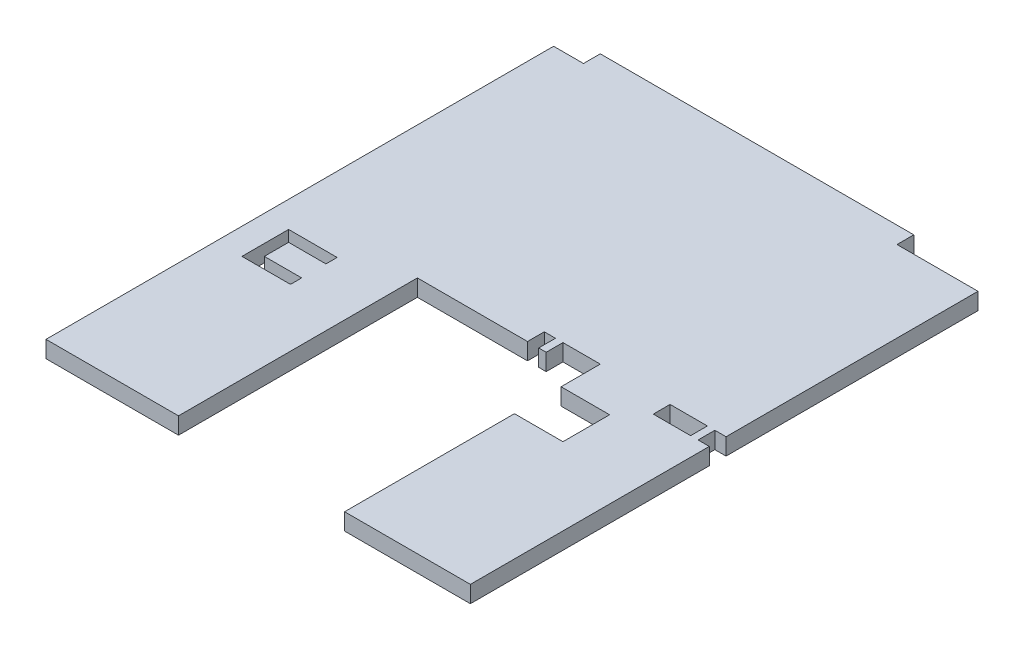
SolidWorks part; units mm, degrees
material "Teak"
ref_plane "Front Plane" through (0, 0, 0) normal (0, 0, 1) x (1, 0, 0)
ref_plane "Top Plane" through (0, 0, 0) normal (0, 1, 0) x (1, 0, 0)
ref_plane "Right Plane" through (0, 0, 0) normal (1, 0, 0) x (0, 0, -1)
sketch "Sketch1" plane through (0, 0, 0) normal (0, 1, 0) x (1, 0, 0)
  line L0 (-33.7045, -15.5) -> (-33.7045, -18.5) construction
  line L1 (46.2955, 72) -> (38.2955, 72) construction
  line L2 (38.2955, 72) -> (38.2955, 76.5) construction
  line L3 (-45.7045, 76.5) -> (-45.7045, 72) construction
  line L4 (-45.7045, 72) -> (-53.7045, 72) construction
  line L5 (-53.7045, -64) -> (-53.7045, 72) construction
  line L6 (-18.2045, -64) -> (-53.7045, -64) construction
  line L7 (-18.2045, -64) -> (-18.2045, 0) construction
  line L8 (-18.2045, 0) -> (11.2955, 0) construction
  line L9 (14.2955, 0) -> (16.2955, 0) construction
  line L10 (26.2955, 0) -> (26.2955, -6) construction
  line L11 (26.2955, -18.5) -> (26.2955, -60) construction
  line L12 (-33.7045, -15.5) -> (-43.7045, -15.5) construction
  line L13 (-46.7045, -6) -> (-33.7045, -6) construction
  line L14 (-46.7045, -18.5) -> (-33.7045, -18.5) construction
  line L15 (-33.7045, -6) -> (-33.7045, -9) construction
  line L16 (-33.7045, -9) -> (-43.7045, -9) construction
  line L17 (39.2955, -6) -> (26.2955, -6) construction
  line L18 (39.2955, -18.5) -> (26.2955, -18.5) construction
  line L19 (-45.7045, 76.5) -> (38.2955, 76.5) construction
  line L20 (26.2955, -60) -> (26.2955, -64) construction
  line L21 (26.2955, -64) -> (46.2955, -64) construction
  line L22 (-46.7045, -6) -> (-46.7045, -18.5) construction
  line L23 (-43.7045, -9) -> (-43.7045, -15.5) construction
  line L24 (39.2955, -6) -> (39.2955, -18.5) construction
  line L25 (46.2955, -64) -> (51.2955, -64) construction
  line L26 (51.2955, 72) -> (46.2955, 72) construction
  line L27 (26.2955, 0) -> (26.2955, 4.5) construction
  line L28 (26.2955, 4.5) -> (16.2955, 4.5) construction
  line L29 (16.2955, 4.5) -> (16.2955, 0) construction
  line L30 (16.2955, 0) -> (14.2955, 0) construction
  line L31 (59.9955, 4.5) -> (56.9955, 4.5) construction
  line L32 (56.9955, 4.5) -> (56.9955, 0) construction
  line L33 (26.2955, -64) -> (51.2955, -64) construction
  line L34 (51.2955, -64) -> (59.9955, -64) construction
  line L35 (59.9955, -64) -> (59.9955, 0) construction
  line L36 (59.9955, 4.5) -> (59.9955, 72) construction
  line L37 (59.9955, 72) -> (51.2955, 72) construction
  line L38 (54.9955, 0) -> (54.9955, 4.5) construction
  line L39 (54.9955, 4.5) -> (44.9955, 4.5) construction
  line L40 (44.9955, 4.5) -> (44.9955, 0) construction
  line L41 (14.2955, 0) -> (14.2955, 4.5) construction
  line L42 (14.2955, 4.5) -> (11.2955, 4.5) construction
  line L43 (11.2955, 4.5) -> (11.2955, 0) construction
  line L44 (44.9955, 0) -> (54.9955, 0) construction
  line L45 (56.9955, 0) -> (59.9955, 0) construction
sketch "Sketch2" plane through (0, 0, 0) normal (0, 1, 0) x (1, 0, 0)
  line L0 (11.2955, 4.5) -> (11.2955, 0) construction
  line L1 (14.2955, 0) -> (16.2955, 0) construction
  line L2 (16.2955, 4.5) -> (16.2955, 0) construction
  line L3 (14.2955, 0) -> (14.2955, 4.5) construction
  line L4 (14.2955, 4.5) -> (11.2955, 4.5) construction
  line L5 (26.2955, 4.5) -> (16.2955, 4.5) construction
  line L6 (54.9955, 4.5) -> (44.9955, 4.5) construction
  line L7 (44.9955, 4.5) -> (44.9955, 0) construction
  line L8 (44.9955, 0) -> (54.9955, 0) construction
  line L9 (56.9955, 0) -> (59.9955, 0) construction
  line L10 (56.9955, 4.5) -> (56.9955, 0) construction
  line L11 (54.9955, 0) -> (54.9955, 4.5) construction
  line L12 (59.9955, 4.5) -> (56.9955, 4.5) construction
  line L13 (39.2955, -6) -> (39.2955, -18.5) construction
  line L14 (39.2955, -18.5) -> (26.2955, -18.5) construction
  line L15 (39.2955, -6) -> (26.2955, -6) construction
  line L16 (-33.7045, -15.5) -> (-33.7045, -18.5) construction
  line L17 (-33.7045, -6) -> (-33.7045, -9) construction
  line L18 (-33.7045, -9) -> (-43.7045, -9) construction
  line L19 (-43.7045, -9) -> (-43.7045, -15.5) construction
  line L20 (-33.7045, -15.5) -> (-43.7045, -15.5) construction
  line L21 (-46.7045, -18.5) -> (-33.7045, -18.5) construction
  line L22 (-46.7045, -6) -> (-46.7045, -18.5) construction
  line L23 (-46.7045, -6) -> (-33.7045, -6) construction
  line L24 (-18.2045, 0) -> (11.2955, 0) construction
  line L25 (-18.2045, -64) -> (-18.2045, 0) construction
  line L26 (-18.2045, -64) -> (-53.7045, -64) construction
  line L27 (59.9955, -64) -> (59.9955, 0) construction
  line L28 (59.9955, 4.5) -> (59.9955, 72) construction
  line L29 (38.2955, 72) -> (38.2955, 76.5) construction
  line L30 (-53.7045, -64) -> (-53.7045, 72) construction
  line L31 (-45.7045, 72) -> (-53.7045, 72) construction
  line L32 (-45.7045, 76.5) -> (-45.7045, 72) construction
  line L33 (-45.7045, 76.5) -> (38.2955, 76.5) construction
  line L34 (11.2955, 4.5) -> (11.2955, 0)
  line L35 (14.2955, 0) -> (16.2955, 0)
  line L36 (16.2955, 4.5) -> (16.2955, 0)
  line L37 (14.2955, 0) -> (14.2955, 4.5)
  line L38 (14.2955, 4.5) -> (11.2955, 4.5)
  line L39 (26.2955, 4.5) -> (16.2955, 4.5)
  line L40 (54.9955, 4.5) -> (44.9955, 4.5)
  line L41 (44.9955, 4.5) -> (44.9955, 0)
  line L42 (44.9955, 0) -> (54.9955, 0)
  line L43 (56.9955, 0) -> (59.9955, 0)
  line L44 (56.9955, 4.5) -> (56.9955, 0)
  line L45 (54.9955, 0) -> (54.9955, 4.5)
  line L46 (59.9955, 4.5) -> (56.9955, 4.5)
  line L47 (39.2955, -6) -> (39.2955, -18.5)
  line L48 (39.2955, -18.5) -> (26.2955, -18.5)
  line L49 (39.2955, -6) -> (26.2955, -6)
  line L50 (-33.7045, -15.5) -> (-33.7045, -18.5)
  line L51 (-33.7045, -6) -> (-33.7045, -9)
  line L52 (-33.7045, -9) -> (-43.7045, -9)
  line L53 (-43.7045, -9) -> (-43.7045, -15.5)
  line L54 (-33.7045, -15.5) -> (-43.7045, -15.5)
  line L55 (-46.7045, -18.5) -> (-33.7045, -18.5)
  line L56 (-46.7045, -6) -> (-46.7045, -18.5)
  line L57 (-46.7045, -6) -> (-33.7045, -6)
  line L58 (-18.2045, 0) -> (11.2955, 0)
  line L59 (-18.2045, -64) -> (-18.2045, 0)
  line L60 (-18.2045, -64) -> (-53.7045, -64)
  line L61 (59.9955, -64) -> (59.9955, 0)
  line L62 (59.9955, 4.5) -> (59.9955, 72)
  line L63 (38.2955, 72) -> (38.2955, 76.5)
  line L64 (-53.7045, -64) -> (-53.7045, 72)
  line L65 (-45.7045, 72) -> (-53.7045, 72)
  line L66 (-45.7045, 76.5) -> (-45.7045, 72)
  line L67 (-45.7045, 76.5) -> (38.2955, 76.5)
  line L68 (26.2955, 4.5) -> (26.2955, -6)
  line L69 (26.2955, -18.5) -> (26.2955, -64)
  line L70 (26.2955, -64) -> (59.9955, -64)
  line L71 (38.2955, 72) -> (59.9955, 72)
extrude "Boss-Extrude1" add sketch "Sketch2" along normal blind 4.5
